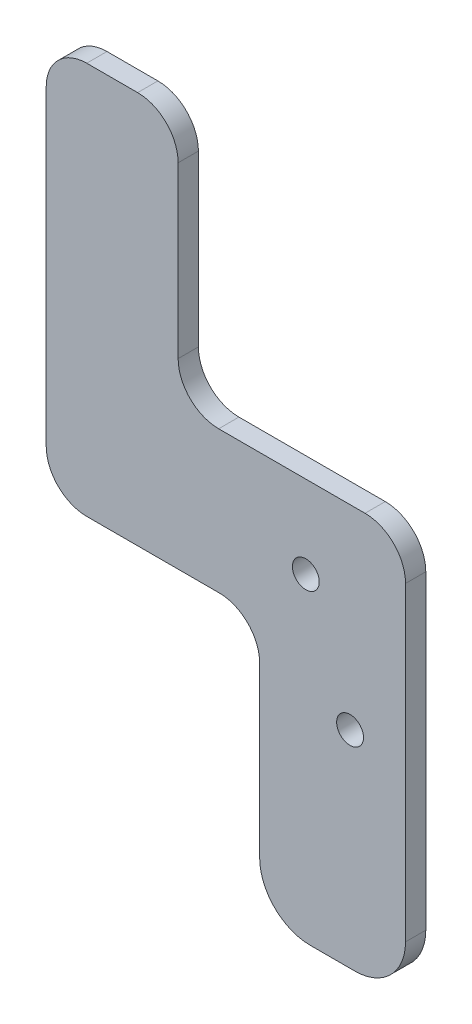
SolidWorks part; units mm, degrees
ref_plane "Front Plane" through (0, 0, 0) normal (0, 0, 1) x (1, 0, 0)
ref_plane "Top Plane" through (0, 0, 0) normal (0, 1, 0) x (1, 0, 0)
ref_plane "Right Plane" through (0, 0, 0) normal (1, 0, 0) x (0, 0, -1)
sketch "Sketch1" plane through (0, 0, 0) normal (0, 0, 1) x (1, 0, 0)
  line L1 (-63.2759, -253.8551) -> (-34.4731, -253.8551)
  line L2 (-63.2759, -253.8551) -> (-63.2759, -384.9337)
  line L3 (-63.2759, -384.9337) -> (-34.4731, -384.9337)
  line L4 (-34.4731, -253.8551) -> (-34.4731, -384.9337)
extrude "Boss-Extrude1" add sketch "Sketch1" along normal blind 4
hole_wizard "M5 Clearance Hole1" positions "Sketch4" profile "Sketch2" hole size "M5" standard "ISO" end condition through all
sketch "Sketch4" plane through (0, 0, 4) normal (0, 0, 1) x (1, 0, 0)
  point P0 (-54.1627, -321.9157)
  point P2 (-54.1627, -293.4157)
sketch "Sketch2" plane through (-54.1627, -321.9157, 4) normal (1, 0, 0) x (0, -1, 0)
  line L0 (0, 0) -> (0, 4)
  line L1 (0, 4) -> (2.65, 4)
  line L2 (2.65, 4) -> (2.65, 0)
  line L5 (2.65, 0) -> (0, 0)
  line L11 (0, -6.35) -> (0, 107.95) construction
  dimension "Thru Hole Dia." = 5.3
  dimension "Thru Hole Depth" = 4
fillet "Fillet1" radius 10 4 edges at (-63.2759, -253.8551, 2) (-34.4731, -253.8551, 2) (-63.2759, -384.9337, 2) (-34.4731, -384.9337, 2)
hole_wizard "M5 Clearance Hole2" positions "Sketch6" profile "Sketch5" hole size "M5" standard "ISO" end condition through all
sketch "Sketch6" plane through (0, 0, 0) normal (0, 0, -1) x (-1, 0, 0)
  point P0 (45.4264, -344.1655)
sketch "Sketch5" plane through (-45.4264, -344.1655, 0) normal (1, 0, 0) x (0, 1, 0)
  line L0 (0, 0) -> (0, 4)
  line L1 (0, 4) -> (2.65, 4)
  line L2 (2.65, 4) -> (2.65, 0)
  line L5 (2.65, 0) -> (0, 0)
  line L11 (0, -6.35) -> (0, 107.95) construction
  dimension "Thru Hole Dia." = 5.3
  dimension "Thru Hole Depth" = 4
sketch "Sketch7" plane through (0, 0, 4) normal (0, 0, 1) x (1, 0, 0)
  line L0 (-63.2759, -263.8551) -> (-63.2759, -374.9337) construction
  line L1 (-63.2759, -333.6557) -> (-105.4252, -333.6557)
  line L2 (-63.2759, -333.6557) -> (-63.2759, -305.6397)
  line L3 (-79.3727, -256.1535) -> (-105.4252, -256.1535)
  line L4 (-105.4252, -333.6557) -> (-105.4252, -256.1535)
  line L7 (-63.2759, -305.6397) -> (-79.3727, -305.6397)
  line L8 (-79.3727, -256.1535) -> (-79.3727, -305.6397)
extrude "Boss-Extrude2" add sketch "Sketch7" against normal up to surface (4 mm away) up to face at (-48.0764, -344.1655, 0)
sketch "Sketch8" plane through (0, 0, 0) normal (0, 0, -1) x (-1, 0, 0)
  line L0 (79.3727, -305.6397) -> (63.2759, -305.6397) construction
  line L1 (71.3243, -251.637) -> (23.8623, -251.637)
  line L2 (71.3243, -251.637) -> (71.3243, -305.6397)
  line L3 (71.3243, -305.6397) -> (23.8623, -305.6397)
  line L4 (23.8623, -251.637) -> (23.8623, -305.6397)
extrude "Cut-Extrude1" cut sketch "Sketch8" against normal blind 14.4
fillet "Fillet2" radius 8 6 edges at (-63.2759, -333.6557, 2) (-105.4252, -333.6557, 2) (-105.4252, -256.1535, 2) (-79.3727, -256.1535, 2) (-79.3727, -305.6397, 2) (-34.4731, -305.6397, 2)
